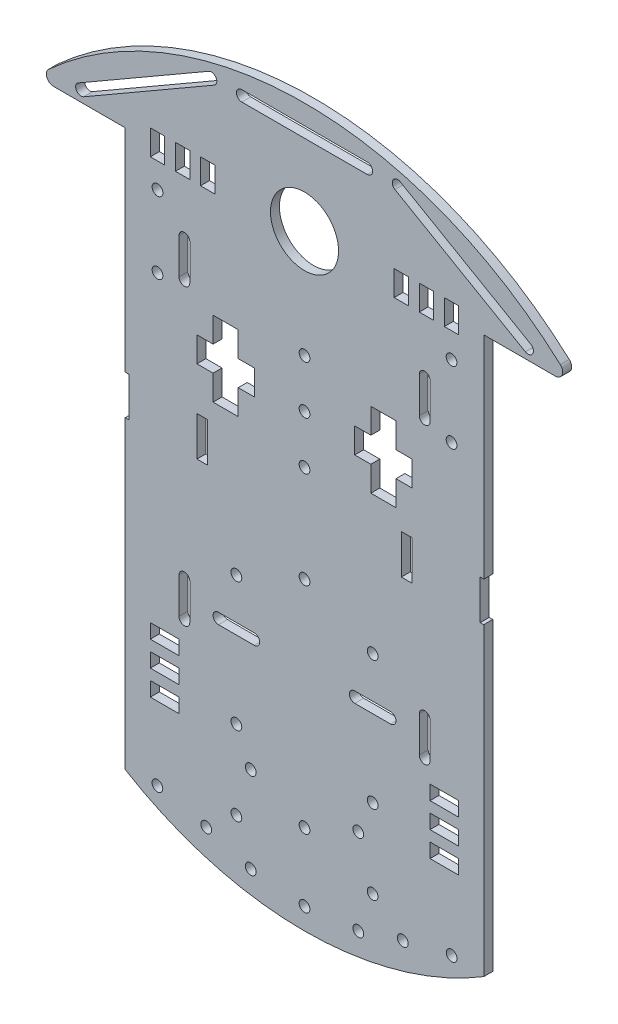
SolidWorks part; units mm, degrees
material "Acrylique (impact moyen-haut)"
ref_plane "Plan de face" through (0, 0, 0) normal (0, 0, 1) x (1, 0, 0)
ref_plane "Plan de dessus" through (0, 0, 0) normal (0, 1, 0) x (1, 0, 0)
ref_plane "Plan de droite" through (0, 0, 0) normal (1, 0, 0) x (0, 0, -1)
sketch "Esquisse1" plane through (0, 0, 0) normal (0, 0, 1) x (1, 0, 0)
  line L0 (100, 155) -> (119.9942, 155)
  line L1 (100, 77.5) -> (0, 77.5) construction
  line L2 (0, 0) -> (0, 155)
  line L3 (0, 155) -> (-19.9942, 155)
  line L4 (100, 0) -> (100, 155)
  line L5 (125, 155) -> (-25, 155) construction
  line L6 (125, 186) -> (-25, 186) construction
  line L7 (50, -14) -> (169.1274, -14) construction
  line L8 (50, 155) -> (50, 123.7315) construction
  arc A0 (121.3374, 158.4819) -> (-21.3374, 158.4819) centre (50, 79.7742) ccw
  arc A1 (100, 0) -> (0, 0) centre (50, 82.2857) cw
  arc A2 (-21.3374, 158.4819) -> (-19.9942, 155) centre (-19.9942, 157) ccw
  arc A3 (119.9942, 155) -> (121.3374, 158.4819) centre (119.9942, 157) ccw
  dimension "D3" = 200
  dimension "D5" = 31
  dimension "D1" = 2
  dimension "D2" = 100
  dimension "D4" = 150
  dimension "D6" = 155
extrude "Boss.-Extru.1" add sketch "Esquisse1" along normal blind 2.5 contours L4 L0 A3 A0 A2 L3 L2 A1
sketch "Esquisse2" plane through (0, 0, 0) normal (0, 0, -1) x (-1, 0, 0)
  line L0 (-100, 155) -> (0, 155) construction
  line L1 (-50, 155) -> (-50, 122.9953) construction
  circle A0 centre (-50, 155) radius 9.5
  point P6 (-50, 155)
  dimension "D1" = 19
extrude "Enlèv. mat.-Extru.1" cut sketch "Esquisse2" against normal through all
sketch "Esquisse3" plane through (0, 0, 0) normal (0, 0, -1) x (-1, 0, 0)
  line L1 (-93, 158.5) -> (-89, 158.5)
  line L2 (-93, 158.5) -> (-93, 151.5)
  line L3 (-93, 151.5) -> (-89, 151.5)
  line L4 (-89, 158.5) -> (-89, 151.5)
  line L5 (-100, 0) -> (-100, 155) construction
  line L11 (-100, 155) -> (-88.6993, 155) construction
  point P8 (-93, 155)
  dimension "D1" = 7
  dimension "D2" = 4
  dimension "D3" = 7
extrude "Enlèv. mat.-Extru.2" cut sketch "Esquisse3" against normal through all
pattern_linear "Répétition linéaire1" count 3 spacing 7 along (-1, 0, 0) of "Enlèv. mat.-Extru.2"
sketch "Esquisse4" plane through (0, 0, 0) normal (0, 0, -1) x (-1, 0, 0)
  line L0 (-75.5, 122) -> (-68.5, 122)
  line L1 (-68.5, 122) -> (-68.5, 115)
  line L2 (-68.5, 115) -> (-64, 115)
  line L3 (-64, 115) -> (-64, 108)
  line L4 (-64, 108) -> (-68.5, 108)
  line L5 (-68.5, 108) -> (-68.5, 101)
  line L6 (-68.5, 101) -> (-75.5, 101)
  line L7 (-75.5, 101) -> (-75.5, 108)
  line L8 (-75.5, 108) -> (-80, 108)
  line L9 (-80, 108) -> (-80, 115)
  line L10 (-80, 115) -> (-75.5, 115)
  line L11 (-75.5, 115) -> (-75.5, 122)
  line L12 (-100, 155) -> (-119.9942, 155) construction
  line L13 (-72, 122) -> (-72, 101) construction
  line L14 (-80, 111.5) -> (-64, 111.5) construction
  line L15 (-100, 0) -> (-100, 155) construction
  point P19 (-72, 111.5)
  point P21 (-72, 111.5)
  dimension "D1" = 47
  dimension "D2" = 7
  dimension "D3" = 16
  dimension "D4" = 21
  dimension "D5" = 7
  dimension "D6" = 20
extrude "Enlèv. mat.-Extru.3" cut sketch "Esquisse4" against normal through all
sketch "Esquisse5" plane through (0, 0, 0) normal (0, 0, -1) x (-1, 0, 0)
  line L0 (-80, 108) -> (-75.5, 108) construction
  line L1 (-80, 96) -> (-77, 96)
  line L2 (-80, 96) -> (-80, 85)
  line L3 (-80, 85) -> (-77, 85)
  line L4 (-77, 96) -> (-77, 85)
  line L5 (-100, 0) -> (-100, 155) construction
  dimension "D1" = 12
  dimension "D2" = 3
  dimension "D3" = 11
  dimension "D4" = 20
extrude "Enlèv. mat.-Extru.4" cut sketch "Esquisse5" against normal through all
pattern_linear "Répétition linéaire2" count 2 spacing 22 along (1, 0, 0) of "Enlèv. mat.-Extru.4"
sketch "Esquisse6" plane through (0, 0, 0) normal (0, 0, -1) x (-1, 0, 0)
  line L0 (-65, 17.5) -> (-65, 7.0648) construction
  line L1 (-100, 0) -> (-100, 85) construction
  line L2 (-83.5, 54.5) -> (-83.5, 44.5) construction
  line L3 (-82, 54.5) -> (-82, 44.5)
  line L4 (-85, 54.5) -> (-85, 44.5)
  line L5 (-74, 49.5) -> (-64, 49.5) construction
  line L6 (-74, 51) -> (-64, 51)
  line L7 (-74, 48) -> (-64, 48)
  line L8 (-83.5, 136.5) -> (-83.5, 126.5) construction
  line L9 (-82, 136.5) -> (-82, 126.5)
  line L10 (-85, 136.5) -> (-85, 126.5)
  line L11 (-112.3374, 158) -> (-75.9643, 179) construction
  line L12 (-113.0874, 159.299) -> (-76.7143, 180.299)
  line L13 (-111.5874, 156.701) -> (-75.2143, 177.701)
  line L14 (-112.3374, 158) -> (-68.1921, 158) construction
  line L15 (-100, 155) -> (-119.9942, 155) construction
  line L16 (-91, 151.5) -> (-91, 144.5) construction
  line L17 (-93, 151.5) -> (-89, 151.5) construction
  line L19 (-69, 49.5) -> (-69, 65.1561) construction
  line L20 (-50, 89.2969) -> (-50, -6.5) construction
  line L21 (0, 0) -> (0, 155) construction
  circle A0 centre (-91, 144.5) radius 1.5
  arc A1 (-82, 54.5) -> (-85, 54.5) centre (-83.5, 54.5) ccw
  circle A2 centre (-91, 124.5) radius 1.5
  circle A3 centre (-65, 17.5) radius 1.5
  circle A4 centre (-69, 26.5) radius 1.5
  circle A5 centre (-91.03, 0.6026) radius 1.5
  circle A6 centre (-77.4014, -2.6005) radius 1.5
  circle A7 centre (-69, 4.5) radius 1.5
  circle A8 centre (-65, -6.5) radius 1.5
  arc A9 (-85, 44.5) -> (-82, 44.5) centre (-83.5, 44.5) ccw
  arc A10 (-74, 51) -> (-74, 48) centre (-74, 49.5) ccw
  arc A11 (-64, 48) -> (-64, 51) centre (-64, 49.5) ccw
  arc A12 (-82, 136.5) -> (-85, 136.5) centre (-83.5, 136.5) ccw
  arc A13 (-85, 126.5) -> (-82, 126.5) centre (-83.5, 126.5) ccw
  arc A14 (-113.0874, 159.299) -> (-111.5874, 156.701) centre (-112.3374, 158) ccw
  arc A15 (-75.2143, 177.701) -> (-76.7143, 180.299) centre (-75.9643, 179) ccw
  circle A16 centre (-69, 62.5) radius 1.5
  point P21 (-83.5, 49.5)
  point P26 (-69, 49.5)
  point P33 (-83.5, 131.5)
  point P40 (-94.1508, 168.5)
  dimension "D1" = 3
  dimension "D2" = 3
  dimension "D3" = 3
  dimension "D4" = 3
  dimension "D5" = 3
  dimension "D6" = 3
  dimension "D7" = 3
  dimension "D10" = 3
  dimension "D28" = 3
  dimension "D8" = 24
  dimension "D11" = 3
  dimension "D12" = 3
  dimension "D13" = 3
  dimension "D14" = 3
  dimension "D15" = 15
  dimension "D17" = 10
  dimension "D18" = 10
  dimension "D19" = 10
  dimension "D20" = 42
  dimension "D21" = 3
  dimension "D22" = 9
  dimension "D23" = 30
  dimension "D24" = 7
  dimension "D25" = 15
  dimension "D26" = 20
  dimension "D27" = 72
  dimension "D16" = 8
  dimension "D29" = 11.5
  dimension "D30" = 21.5
  dimension "D31" = 137.5
  dimension "D9" = 15
  dimension "D32" = 14
  dimension "D33" = 13
  dimension "D34" = 11
  dimension "D35" = 22
  dimension "D36" = 34
extrude "Enlèv. mat.-Extru.5" cut sketch "Esquisse6" against normal through all
sketch "Esquisse7" plane through (0, 0, 0) normal (0, 0, -1) x (-1, 0, 0)
  line L0 (-100, 0) -> (-100, 85) construction
  line L5 (-93, 39) -> (-85, 39)
  line L6 (-93, 39) -> (-93, 35)
  line L7 (-93, 35) -> (-85, 35)
  line L8 (-85, 39) -> (-85, 35)
  line L9 (-93, 32) -> (-85, 32)
  line L10 (-93, 32) -> (-93, 28)
  line L11 (-93, 28) -> (-85, 28)
  line L12 (-85, 32) -> (-85, 28)
  line L13 (-93, 25) -> (-85, 25)
  line L14 (-93, 25) -> (-93, 21)
  line L15 (-93, 21) -> (-85, 21)
  line L16 (-85, 25) -> (-85, 21)
  arc A0 (-100, 0) -> (0, 0) centre (-50, 82.2857) ccw construction
  point P18 (-50, -14)
  dimension "D6" = 3
  dimension "D7" = 3
  dimension "D1" = 4
  dimension "D2" = 4
  dimension "D3" = 4
  dimension "D4" = 8
  dimension "D5" = 7
  dimension "D8" = 35
extrude "Enlèv. mat.-Extru.6" cut sketch "Esquisse7" against normal through all
ref_plane "Plan1" through (50, 0, 0) normal (1, 0, 0) x (0, 0, -1)
mirror "Symétrie1" about plane through (50, 0, 0) normal (1, 0, 0) of "Répétition linéaire2", "Enlèv. mat.-Extru.2", "Répétition linéaire1", "Enlèv. mat.-Extru.3", "Enlèv. mat.-Extru.4", "Enlèv. mat.-Extru.5", "Enlèv. mat.-Extru.6"
sketch "Esquisse8" plane through (0, 0, 0) normal (0, 0, -1) x (-1, 0, 0)
  line L0 (-67.5, 178.9806) -> (-32.5, 178.9806) construction
  line L1 (-67.5, 180.4806) -> (-32.5, 180.4806)
  line L2 (-67.5, 177.4806) -> (-32.5, 177.4806)
  line L5 (-50, 251.8346) -> (-50, 106.1266) construction
  line L6 (0, 0) -> (0, 85) construction
  line L7 (-100, 96) -> (-100, 155) construction
  line L8 (-64, 111.5) -> (-36, 111.5) construction
  line L9 (-64, 108) -> (-64, 115) construction
  line L10 (-36, 108) -> (-36, 115) construction
  arc A0 (-67.5, 180.4806) -> (-67.5, 177.4806) centre (-67.5, 178.9806) ccw
  arc A1 (-32.5, 177.4806) -> (-32.5, 180.4806) centre (-32.5, 178.9806) ccw
  circle A2 centre (-50, 111.5) radius 1.5
  circle A3 centre (-50, 125) radius 1.5
  circle A4 centre (-50, 98) radius 1.5
  circle A5 centre (-50, 71) radius 1.5
  circle A6 centre (-50, -8) radius 1.5
  circle A7 centre (-50, 11) radius 1.5
  point P2 (-50, 178.9806)
  dimension "D1" = 3
  dimension "D3" = 3
  dimension "D4" = 3
  dimension "D5" = 3
  dimension "D6" = 3
  dimension "D7" = 3
  dimension "D11" = 3
  dimension "D2" = 35
  dimension "D8" = 13.5
  dimension "D9" = 13.5
  dimension "D10" = 27
  dimension "D12" = 60
  dimension "D13" = 19
extrude "Enlèv. mat.-Extru.7" cut sketch "Esquisse8" against normal blind 10
equation "\"D2@Esquisse6\"=\"D1@Esquisse6\""
equation "\"D3@Esquisse6\"=\"D2@Esquisse6\""
equation "\"D4@Esquisse6\"=\"D2@Esquisse6\""
equation "\"D5@Esquisse6\"=\"D2@Esquisse6\""
equation "\"D6@Esquisse6\"=\"D2@Esquisse6\""
equation "\"D7@Esquisse6\"=\"D2@Esquisse6\""
equation "\"D2@Esquisse7\"=\"D1@Esquisse7\""
equation "\"D3@Esquisse7\"=\"D1@Esquisse7\""
equation "\"D10@Esquisse6\"=\"D7@Esquisse6\""
equation "\"D12@Esquisse6\"=\"D11@Esquisse6\""
equation "\"D13@Esquisse6\"=\"D11@Esquisse6\""
equation "\"D14@Esquisse6\"=\"D11@Esquisse6\""
equation "\"D17@Esquisse6\"=\"D19@Esquisse6\""
equation "\"D18@Esquisse6\"=\"D19@Esquisse6\""
equation "\"D28@Esquisse6\"=\"D1@Esquisse6\""
equation "\"D4@Esquisse8\"=\"D3@Esquisse8\""
equation "\"D5@Esquisse8\"=\"D3@Esquisse8\""
equation "\"D6@Esquisse8\"=\"D3@Esquisse8\""
equation "\"D7@Esquisse8\"=\"D3@Esquisse8\""
equation "\"D11@Esquisse8\"=\"D6@Esquisse8\""
